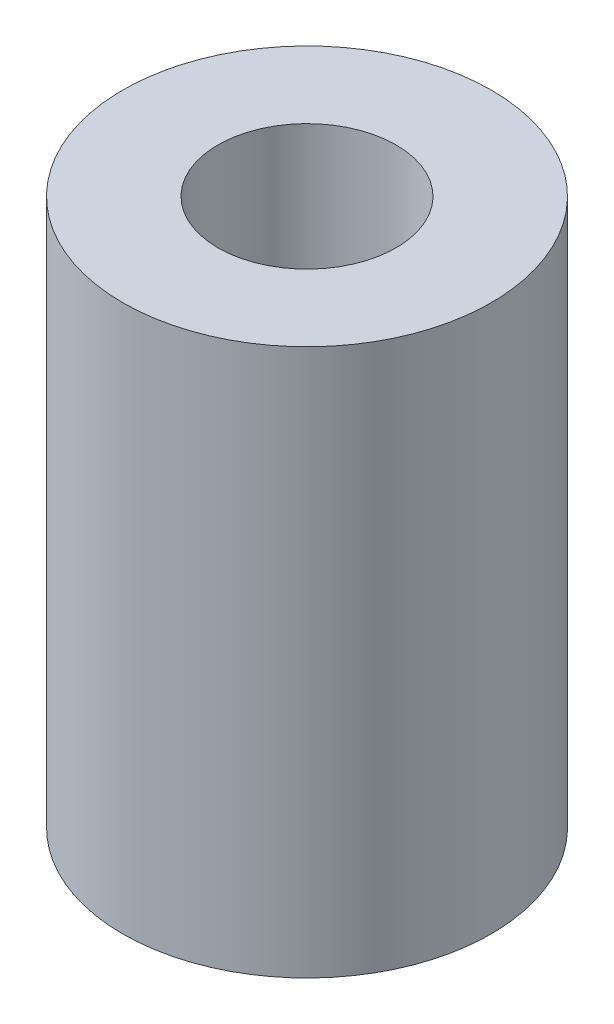
SolidWorks part; units mm, degrees
ref_plane "Front Plane" through (0, 0, 0) normal (0, 0, 1) x (1, 0, 0)
ref_plane "Top Plane" through (0, 0, 0) normal (0, 1, 0) x (1, 0, 0)
ref_plane "Right Plane" through (0, 0, 0) normal (1, 0, 0) x (0, 0, -1)
sketch "Sketch1" plane through (0, 0, 0) normal (0, 1, 0) x (1, 0, 0)
  circle A0 centre (0, 0) radius 3.75
  circle A1 centre (0, 0) radius 7.75
  dimension "D1" = 7.5
  dimension "D2" = 4
extrude "Boss-Extrude1" add sketch "Sketch1" along normal blind 23 contours A1 | A0
